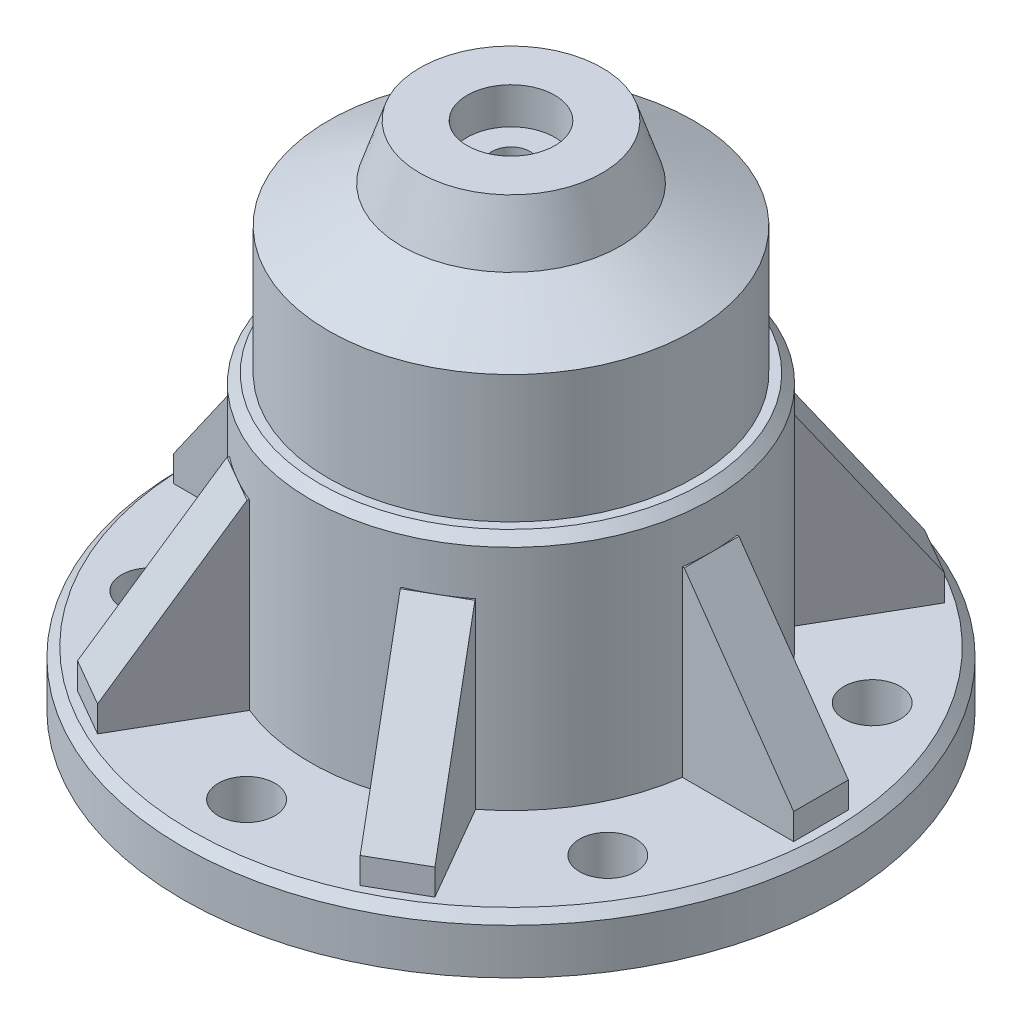
SolidWorks part; units mm, degrees
ref_plane "Front Plane" through (0, 0, 0) normal (0, 0, 1) x (1, 0, 0)
ref_plane "Top Plane" through (0, 0, 0) normal (0, 1, 0) x (1, 0, 0)
ref_plane "Right Plane" through (0, 0, 0) normal (1, 0, 0) x (0, 0, -1)
sketch "Sketch1" plane through (0, 0, 0) normal (0, 1, 0) x (1, 0, 0)
  circle A0 centre (0, 0) radius 8
  circle A1 centre (0, 0) radius 18
  dimension "D1" = 16
  dimension "D2" = 10
extrude "Boss-Extrude1" add sketch "Sketch1" along normal blind 3
sketch "Sketch2" plane through (0, 3, 0) normal (0, 1, 0) x (1, 0, 0)
  circle A0 centre (0, 0) radius 11
  circle A1 centre (0, 0) radius 8 construction
  circle A2 centre (0, 0) radius 8
  dimension "D1" = 3
extrude "Boss-Extrude2" add sketch "Sketch2" along normal blind 22 contours A0
sketch "Sketch3" plane through (0, 3, 0) normal (0, 1, 0) x (1, 0, 0)
  line L0 (0, 0) -> (18, 0) construction
  line L1 (0, 0) -> (15.5885, -9) construction
  line L2 (9.5263, -5.5) -> (15.5885, -9) construction
  circle A0 centre (0, 0) radius 18 construction
  circle A1 centre (0, 0) radius 11 construction
  circle A2 centre (0, 0) radius 11
  point P10 (12.5574, -7.25)
  point P14 (0, -14.5)
  point P15 (-12.5574, -7.25)
  point P16 (-12.5574, 7.25)
  point P17 (0, 14.5)
  point P18 (12.5574, 7.25)
  point P19 (0, 0)
  dimension "D1" = 30
  dimension "D2" = 6
ref_point "Point1"
ref_point "Point2"
ref_point "Point3"
hole_wizard "M (0.295) Diameter Hole1" positions "3DSketch1" profile "Sketch4" hole size "M" standard "ANSI Inch" end condition through all
sketch3d "3DSketch1"
  point P0 (0, 3, 14.5)
  point P3 (-12.5574, 3, 7.25)
  point P6 (12.5574, 3, 7.25)
  point P9 (12.5574, 3, -7.25)
  point P12 (0, 3, -14.5)
  point P15 (-12.5574, 3, -7.25)
sketch "Sketch4" plane through (0, 3, 14.5) normal (1, 0, 0) x (0, 0, 1)
  line L0 (0, 0) -> (0, 3)
  line L1 (0, 3) -> (1.55, 3)
  line L2 (1.55, 3) -> (1.55, 0)
  line L5 (1.55, 0) -> (0, 0)
  line L11 (0, -6.35) -> (0, 107.95) construction
  dimension "Thru Hole Dia." = 3.1
  dimension "Thru Hole Depth" = 3
ref_plane "Plane1" through (0, 0, 0) normal (0, 0, 1) x (1, 0, 0)
sketch "Sketch5" plane through (0, 0, 0) normal (0, 0, 1) x (1, 0, 0)
  line L0 (18, 3) -> (11, 13) construction
  line L1 (11, 3) -> (11, 25) construction
  line L2 (11, 3) -> (-11, 3) construction
  line L3 (11, 13) -> (17, 4.4286)
  line L5 (17, 4.4286) -> (17, 3)
  line L6 (17, 3) -> (17, 2.5)
  line L7 (11, 13) -> (10.5, 13)
  line L9 (10.5, 13) -> (10.5, 2.5)
  line L10 (10.5, 2.5) -> (17, 2.5)
  dimension "D1" = 10
  dimension "D2" = 1
  dimension "D3" = 0.5
  dimension "D4" = 0.5
extrude "Boss-Extrude3" add sketch "Sketch5" along normal mid plane 3
ref_axis "Axis1" through (0, 18, 0) along (0, -1, 0)
pattern_circular "CirPattern1" count 6 over 360 about axis through (0, 0, 0) along (0, 1, 0) of "Boss-Extrude3"
chamfer "Chamfer2" distance 0.5 angle 45 1 edges at (0, 3, 18)
sketch "Sketch6" plane through (0, 25, 0) normal (0, 1, 0) x (1, 0, 0)
  circle A0 centre (0, 0) radius 11
extrude "Boss-Extrude4" add sketch "Sketch6" along normal blind 3
sketch "Sketch8" plane through (0, 25, 0) normal (0, -1, 0) x (1, 0, 0)
  circle A1 centre (0, 0) radius 8
  circle A2 centre (0, 0) radius 8
  dimension "D1" = 0
extrude "Boss-Extrude5" add sketch "Sketch8" along normal blind 2
chamfer "Chamfer3" distance 6 angle 45 1 edges at (0, 28, 11)
sketch "Sketch7" plane through (0, 28, 0) normal (0, 1, 0) x (1, 0, 0)
  circle A0 centre (0, 0) radius 2.4
  dimension "D1" = 4.8
extrude "Cut-Extrude1" cut sketch "Sketch7" against normal blind 2
sketch "Sketch9" plane through (0, 26, 0) normal (0, 1, 0) x (1, 0, 0)
  circle A0 centre (0, 0) radius 1.05
  dimension "D1" = 2.1
extrude "Cut-Extrude2" cut sketch "Sketch9" against normal up to next
sketch "Sketch10" plane through (0, 28, 0) normal (0, 1, 0) x (1, 0, 0)
  circle A0 centre (0, 0) radius 10
  circle A1 centre (0, 0) radius 11 construction
  circle A2 centre (0, 0) radius 11
  dimension "D1" = 1
extrude "Cut-Extrude3" cut sketch "Sketch10" against normal blind 12
chamfer "Chamfer4" distance 0.5 angle 45 1 edges at (0, 16, 11)
sketch "Sketch11" plane through (0, 0, 0) normal (0, 0, 1) x (1, 0, 0)
  line L3 (-5, 28) -> (-5, 29.2576)
  line L4 (-5, 28) -> (-5.9897, 25.0175)
  line L5 (-5.9897, 25.0175) -> (-10, 23)
  line L6 (-5, 29.2576) -> (-10, 29.2576)
  line L7 (-10, 29.2576) -> (-10, 23)
revolve "Cut-Revolve1" cut sketch "Sketch11" angle 360 about axis through (0, 18, 0) along (0, -1, 0)
chamfer "Chamfer5" distance 2 angle 60 1 edges at (0, 23, -8)
